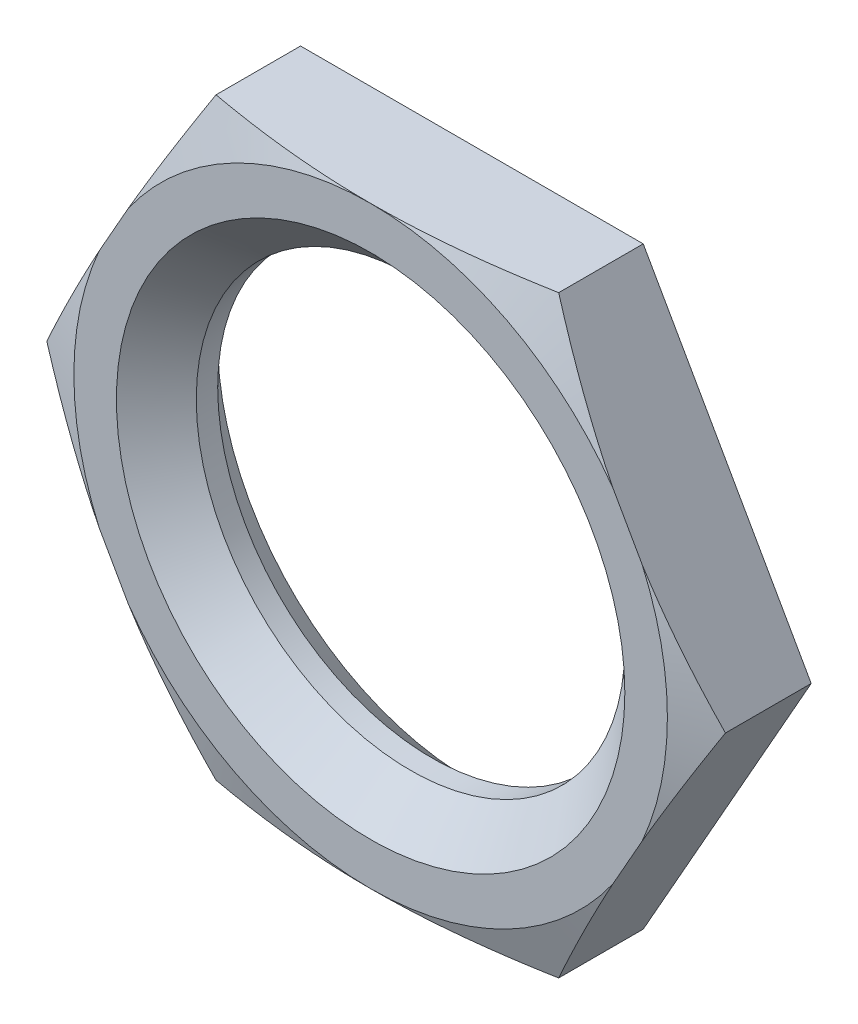
SolidWorks part; units mm, degrees
ref_plane "Front Plane" through (0, 0, 0) normal (0, 0, 1) x (1, 0, 0)
ref_plane "Top Plane" through (0, 0, 0) normal (0, 1, 0) x (1, 0, 0)
ref_plane "Right Plane" through (0, 0, 0) normal (1, 0, 0) x (0, 0, -1)
ref_plane "Plane1" through (0, 0, 0) normal (1, 0, 0) x (0, 0, -1)
sketch "Sketch1" plane through (0, 0, 0) normal (1, 0, 0) x (0, 0, -1)
  line L0 (-1.1938, 0) -> (-1.1938, 6.9977)
  line L1 (-1.1938, 6.9977) -> (-0.6844, 8.3972)
  line L2 (-0.6844, 8.3972) -> (1.1938, 8.3972)
  line L3 (1.1938, 8.3972) -> (1.1938, 0)
  line L4 (1.1938, 0) -> (-1.1938, 0)
  line L5 (1.1938, 0) -> (-1.1938, 0) construction
revolve "Revolve1" add sketch "Sketch1" angle 360 about L5
ref_plane "Plane2" through (0, 0, 0) normal (0, 0, 1) x (1, 0, 0)
sketch "Sketch2" plane through (0, 0, 0) normal (0, 0, 1) x (1, 0, 0)
  line L0 (-13.9954, 13.9954) -> (-13.9954, -13.9954)
  line L1 (-13.9954, -13.9954) -> (13.9954, -13.9954)
  line L2 (13.9954, -13.9954) -> (13.9954, 13.9954)
  line L3 (13.9954, 13.9954) -> (-13.9954, 13.9954)
  line L4 (-8.001, 0) -> (-4.0401, -6.9977)
  line L5 (-4.0401, -6.9977) -> (4.0401, -6.9977)
  line L6 (4.0401, -6.9977) -> (8.001, 0)
  line L7 (8.001, 0) -> (4.0401, 6.9977)
  line L8 (4.0401, 6.9977) -> (-4.0401, 6.9977)
  line L9 (-4.0401, 6.9977) -> (-8.001, 0)
extrude "Cut-Extrude1" cut sketch "Sketch2" against normal blind 2.3876 and the other way blind 2.3876
ref_plane "Plane3" through (0, 0, 0) normal (1, 0, 0) x (0, 0, -1)
sketch "Sketch3" plane through (0, 0, 0) normal (1, 0, 0) x (0, 0, -1)
  line L0 (-1.1938, 0) -> (-1.1938, 5.9944)
  line L1 (-1.1938, 5.9944) -> (-0.2524, 5.053)
  line L2 (-0.2524, 5.053) -> (0.2524, 5.053)
  line L3 (0.2524, 5.053) -> (1.1938, 5.9944)
  line L4 (1.1938, 5.9944) -> (1.1938, 0)
  line L5 (1.1938, 0) -> (-1.1938, 0)
  line L6 (1.1938, 0) -> (-1.1938, 0) construction
revolve "Cut-Revolve1" cut sketch "Sketch3" angle 360 about L6
